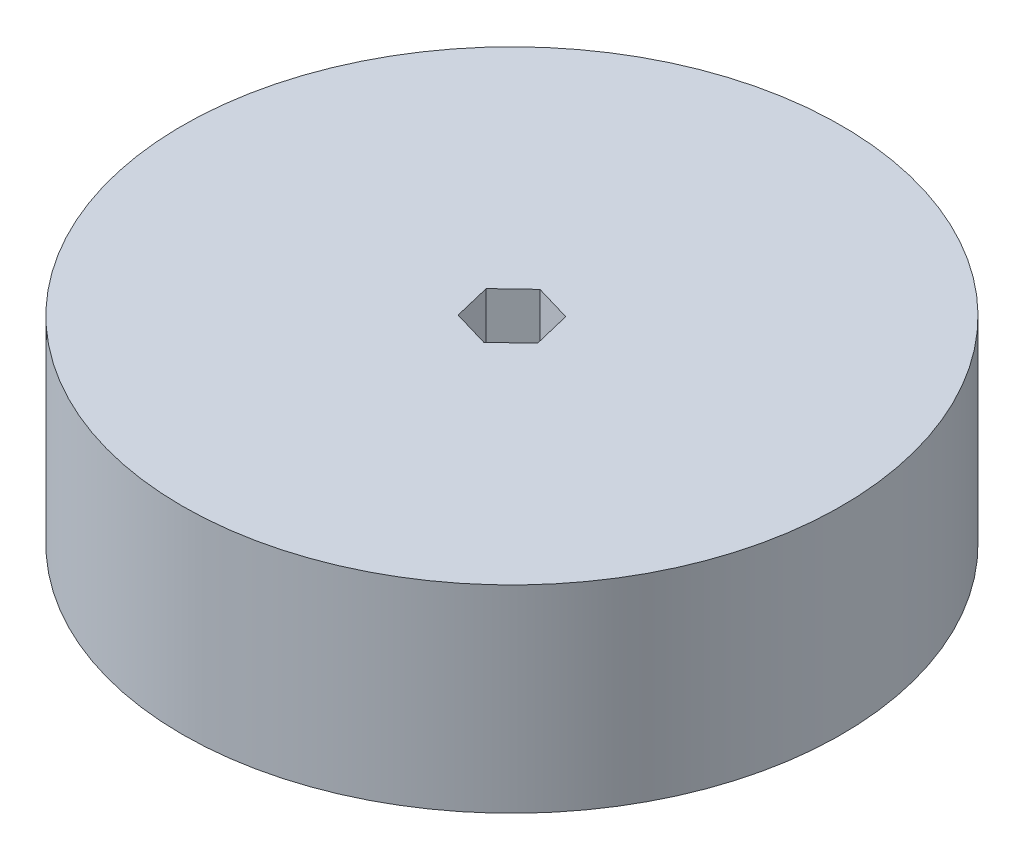
SolidWorks part; units mm, degrees
material "ALUMINUM 6061-T6"
ref_plane "Front Plane" through (0, 0, 0) normal (0, 0, 1) x (1, 0, 0)
ref_plane "Top Plane" through (0, 0, 0) normal (0, 1, 0) x (1, 0, 0)
ref_plane "Right Plane" through (0, 0, 0) normal (1, 0, 0) x (0, 0, -1)
sketch "Sketch1" plane through (0, 0, 0) normal (0, 1, 0) x (1, 0, 0)
  line L0 (-36.8216, -51.7341) -> (36.8216, 51.7341) construction
  line L2 (-7.0333, 2.0728) -> (-5.3117, -5.0546)
  line L3 (-5.3117, -5.0546) -> (1.7215, -7.1274)
  line L4 (1.7215, -7.1274) -> (7.0333, -2.0728)
  line L5 (7.0333, -2.0728) -> (5.3117, 5.0546)
  line L6 (5.3117, 5.0546) -> (-1.7215, 7.1274)
  line L7 (-1.7215, 7.1274) -> (-7.0333, 2.0728)
  circle A0 centre (0, 0) radius 63.5
  circle A1 centre (0, 0) radius 6.35 construction
  dimension "D1" = 127
  dimension "D2" = 12.7
extrude "Boss-Extrude1" add sketch "Sketch1" along normal mid plane 38.1
